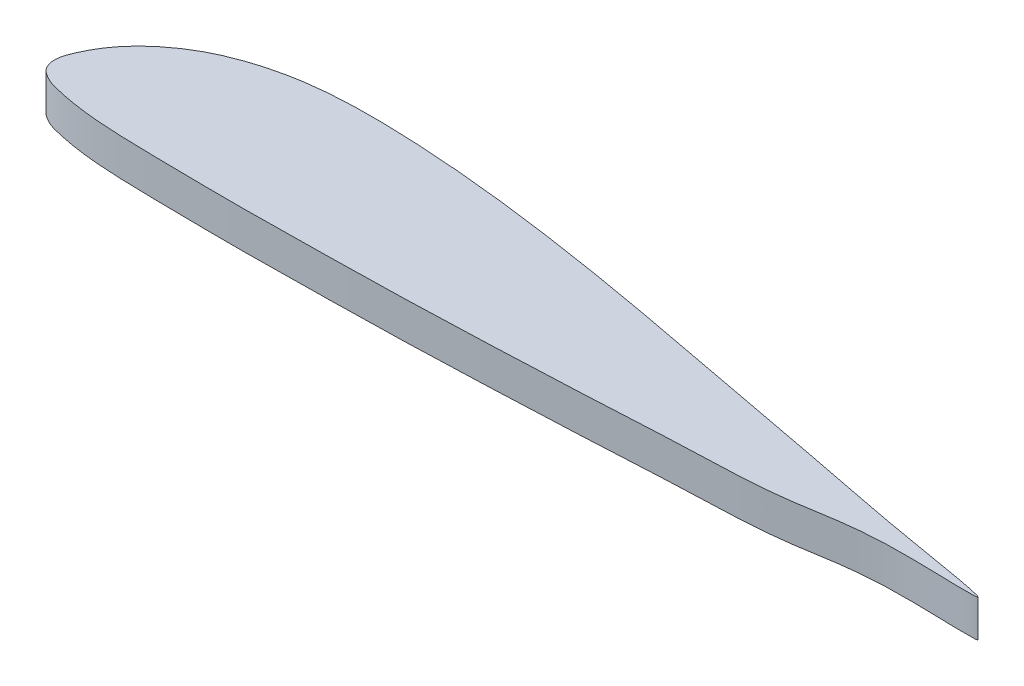
SolidWorks part; units mm, degrees
ref_plane "Front Plane" through (0, 0, 0) normal (0, 0, 1) x (1, 0, 0)
ref_plane "Top Plane" through (0, 0, 0) normal (0, 1, 0) x (1, 0, 0)
ref_plane "Right Plane" through (0, 0, 0) normal (1, 0, 0) x (0, 0, -1)
sketch "Sketch2" plane through (0, 0, 0) normal (0, 1, 0) x (1, 0, 0)
  line L0 (0, 0) -> (100, 0) construction
  spline S0 degree 3 poles (88.4175, 0.541) (105.7801, -0.646) (88.4238, 2.0772) (80.4225, 3.7533) (69.8862, 5.7094) (60.0387, 7.6078) (50.0167, 9.4488) (40.0326, 10.974) (31.6814, 11.8576) (25.0037, 12.2188) (19.9913, 12.2559) (14.932, 11.8315) (10.5527, 10.7172) (7.226, 9.2643) (4.8941, 7.7409) (3.2273, 6.3021) (1.9076, 4.7846) (1.0905, 3.5176) (0.3111, 1.9497) (-0.2747, 0.388) (0.3224, -0.986) (1.1281, -1.5533) (1.9607, -1.9804) (3.3251, -2.3144) (4.9885, -2.6515) (7.3259, -2.9608) (10.6627, -3.1833) (14.9997, -3.2523) (19.9997, -3.318) (25.0003, -3.3357) (31.6666, -3.2336) (40.0045, -3.1188) (49.9937, -2.7479) (60.0321, -2.3291) (69.8873, -1.7353) (80.4502, -1.5289) (88.4175, 0.541) (105.7801, -0.646) (88.4238, 2.0772) knots -0.144975 -0.096715 -0.048179 0 0.049041 0.098082 0.147123 0.196163 0.245117 0.293835 0.342264 0.366386 0.390475 0.414675 0.439566 0.455415 0.466908 0.479712 0.48709 0.495937 0.501323 0.512663 0.51831 0.521365 0.526752 0.531755 0.541582 0.551305 0.565797 0.589895 0.613986 0.638076 0.662167 0.710354 0.75856 0.806786 0.855025 0.903285 0.951821 1 1.049041 1.098082 1.147123 only from (100, 0) to (100, 0)
  point P3 (0.5, 2.3)
  point P4 (1, 3.3)
  point P5 (2, 4.84)
  point P6 (3, 6)
  point P7 (5, 7.75)
  point P8 (7, 9.05)
  point P9 (10, 10.4)
  point P10 (15, 11.7)
  point P11 (20, 12.18)
  point P12 (25, 12.18)
  point P13 (30, 11.92)
  point P14 (40, 10.9)
  point P15 (60, -2.3)
  point P16 (50, -2.74)
  point P17 (40, -3.08)
  point P18 (30, -3.26)
  point P19 (25, -3.32)
  point P20 (20, -3.31)
  point P21 (15, -3.25)
  point P22 (10, -3.12)
  point P23 (7, -2.9)
  point P24 (5, -2.63)
  point P25 (3, -2.23)
  point P26 (2, -1.95)
  point P27 (1, -1.45)
  point P28 (0.5, -1.06)
  point P29 (50, 9.4)
  point P30 (70, 5.7)
  point P31 (60, 7.6)
  point P32 (80, 3.8)
  point P33 (90, 1.9)
  point P34 (100, 0)
  point P35 (70, -1.8)
  point P36 (80, -1.22)
  point P37 (90, -0.0001)
  dimension "D1" = 100
  dimension "D3" = 1
  dimension "D4" = 2
  dimension "D5" = 3
  dimension "D6" = 5
  dimension "D7" = 7
  dimension "D8" = 10
  dimension "D9" = 15
  dimension "D10" = 20
  dimension "D11" = 25
  dimension "D12" = 30
  dimension "D13" = 40
  dimension "D14" = 50
  dimension "D15" = 70
  dimension "D16" = 60
  dimension "D17" = 80
  dimension "D18" = 90
  dimension "D19" = 100
  dimension "D20" = 2.3
  dimension "D21" = 3.3
  dimension "D22" = 4.84
  dimension "D23" = 6
  dimension "D24" = 7.75
  dimension "D25" = 9.05
  dimension "D26" = 10.4
  dimension "D27" = 11.7
  dimension "D28" = 12.18
  dimension "D29" = 12.18
  dimension "D30" = 11.92
  dimension "D31" = 10.9
  dimension "D32" = 9.4
  dimension "D33" = 7.6
  dimension "D34" = 5.7
  dimension "D35" = 3.8
  dimension "D36" = 1.9
  dimension "D37" = 0
  dimension "D38" = 0.5
  dimension "D39" = 1.06
  dimension "D40" = 1.45
  dimension "D41" = 1.95
  dimension "D42" = 2.23
  dimension "D43" = 2.63
  dimension "D44" = 2.9
  dimension "D45" = 3.12
  dimension "D46" = 3.25
  dimension "D47" = 3.31
  dimension "D48" = 3.32
  dimension "D49" = 3.26
  dimension "D50" = 3.08
  dimension "D51" = 2.74
  dimension "D52" = 2.3
  dimension "D53" = 1.8
  dimension "D54" = 1.22
  dimension "D55" = 0.0001
extrude "Boss-Extrude2" add sketch "Sketch2" along normal blind 4
